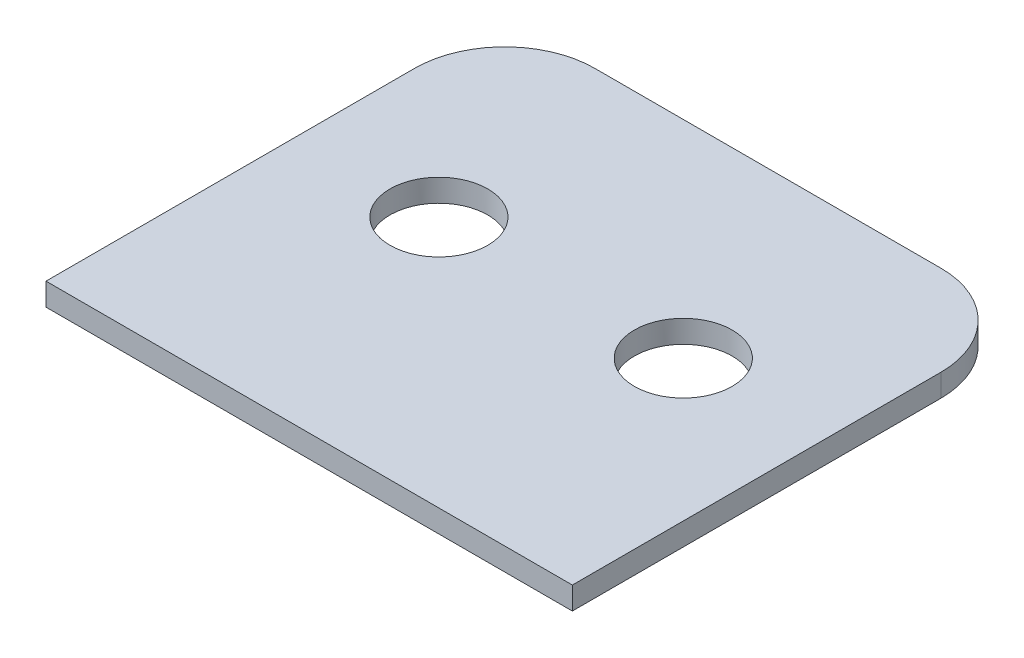
SolidWorks part; units mm, degrees
ref_plane "Front Plane" through (0, 0, 0) normal (0, 0, 1) x (1, 0, 0)
ref_plane "Top Plane" through (0, 0, 0) normal (0, 1, 0) x (1, 0, 0)
ref_plane "Right Plane" through (0, 0, 0) normal (1, 0, 0) x (0, 0, -1)
sketch "Sketch1" plane through (0, 0, 0) normal (0, 1, 0) x (1, 0, 0)
  line L1 (-35, -33.5) -> (35, -33.5)
  line L2 (-35, -33.5) -> (-35, 33.5)
  line L3 (-35, 33.5) -> (35, 33.5)
  line L4 (35, -33.5) -> (35, 33.5)
  line L5 (-35, -33.5) -> (35, 33.5) construction
  line L6 (-35, 33.5) -> (35, -33.5) construction
  point P0 (0, 0)
  dimension "D1" = 67
  dimension "D2" = 70
extrude "Boss-Extrude1" add sketch "Sketch1" along normal blind 3
sketch "Sketch5" plane through (0, 3, 0) normal (0, 1, 0) x (1, 0, 0)
  line L0 (35, -33.5) -> (35, 33.5) construction
  line L1 (-35, 33.5) -> (35, 33.5)
  line L2 (-35, 33.5) -> (-35, 27.5)
  line L3 (-35, 27.5) -> (35, 27.5)
  line L4 (35, 33.5) -> (35, 27.5)
  dimension "D1" = 6
extrude "Cut-Extrude4" cut sketch "Sketch5" against normal through all both and the other way through all
fillet "Fillet1" radius 12 2 edges at (35, 1.5, -27.5) (-35, 1.5, -27.5)
sketch "Sketch2" plane through (0, 3, 0) normal (0, 1, 0) x (1, 0, 0)
  circle A0 centre (-16.25, 0) radius 6.5
  dimension "D1" = 13
  dimension "D2" = 16.25
extrude "Cut-Extrude1" cut sketch "Sketch2" against normal through all both and the other way through all
mirror "Mirror1" about plane through (0, 0, 0) normal (1, 0, 0) of "Cut-Extrude1"
